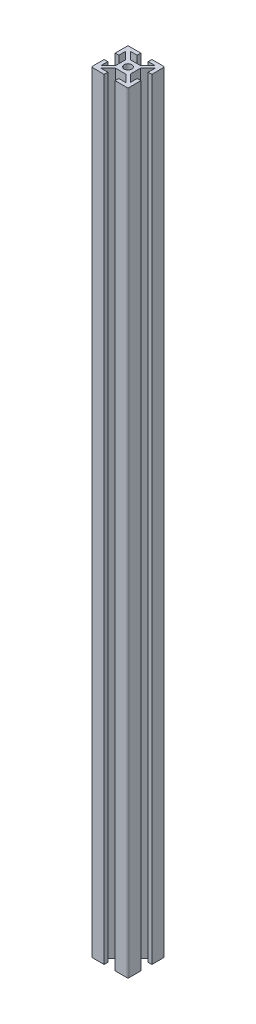
SolidWorks part; units mm, degrees
material "6061 Alloy"
ref_plane "Front Plane" through (0, 0, 0) normal (0, 0, 1) x (1, 0, 0)
ref_plane "Top Plane" through (0, 0, 0) normal (0, 1, 0) x (1, 0, 0)
ref_plane "Right Plane" through (0, 0, 0) normal (1, 0, 0) x (0, 0, -1)
ref_plane "Plane1" through (0, 420, 0) normal (0, 1, 0) x (1, 0, 0)
sketch "Sketch1" plane through (0, 420, 0) normal (0, 1, 0) x (1, 0, 0)
  line L0 (4, 2.7464) -> (8, 6.7464)
  line L1 (8, 6.7464) -> (8, 3)
  line L2 (8, 3) -> (10, 3)
  line L3 (10, 3) -> (10, 9.5)
  line L4 (9.5, 10) -> (3, 10)
  line L5 (3, 10) -> (3, 8)
  line L6 (3, 8) -> (6.8633, 8)
  line L7 (6.8633, 8) -> (2.8633, 4)
  line L8 (2.8633, 4) -> (-2.75, 4)
  line L9 (-2.75, 4) -> (-6.75, 8)
  line L10 (-6.75, 8) -> (-3, 8)
  line L11 (-3, 8) -> (-3, 10)
  line L12 (-3, 10) -> (-9.5, 10)
  line L13 (-10, 9.5) -> (-10, 3)
  line L14 (-10, 3) -> (-8, 3)
  line L15 (-8, 3) -> (-8, 6.75)
  line L16 (-8, 6.75) -> (-4, 2.75)
  line L17 (-4, 2.75) -> (-4, -2.75)
  line L18 (-4, -2.75) -> (-8, -6.75)
  line L19 (-8, -6.75) -> (-8, -3)
  line L20 (-8, -3) -> (-10, -3)
  line L21 (-10, -3) -> (-10, -9.5)
  line L22 (-9.5, -10) -> (-3, -10)
  line L23 (-3, -10) -> (-3, -8)
  line L24 (-3, -8) -> (-6.75, -8)
  line L25 (-6.75, -8) -> (-2.75, -4)
  line L26 (-2.75, -4) -> (2.8685, -4)
  line L27 (2.8685, -4) -> (6.8685, -8)
  line L28 (6.8685, -8) -> (3, -8)
  line L29 (3, -8) -> (3, -10)
  line L30 (3, -10) -> (9.5, -10)
  line L31 (10, -9.5) -> (10, -3)
  line L32 (10, -3) -> (8, -3)
  line L33 (8, -3) -> (8, -6.6652)
  line L34 (8, -6.6652) -> (4, -2.6652)
  line L35 (4, -2.6652) -> (4, 2.7464)
  arc A0 (10, 9.5) -> (9.5, 10) centre (9.5, 9.5) ccw
  arc A1 (-9.5, 10) -> (-10, 9.5) centre (-9.5, 9.5) ccw
  arc A2 (-10, -9.5) -> (-9.5, -10) centre (-9.5, -9.5) ccw
  arc A3 (9.5, -10) -> (10, -9.5) centre (9.5, -9.5) ccw
  circle A4 centre (0, 0) radius 2.1
extrude "Boss-Extrude1" add sketch "Sketch1" against normal blind 420
ref_plane "Plane2" through (0, 0, 0) normal (1, 0, 0) x (0, 0, -1)
ref_plane "Plane3" through (0, 0, 0) normal (0, 0, 1) x (1, 0, 0)
